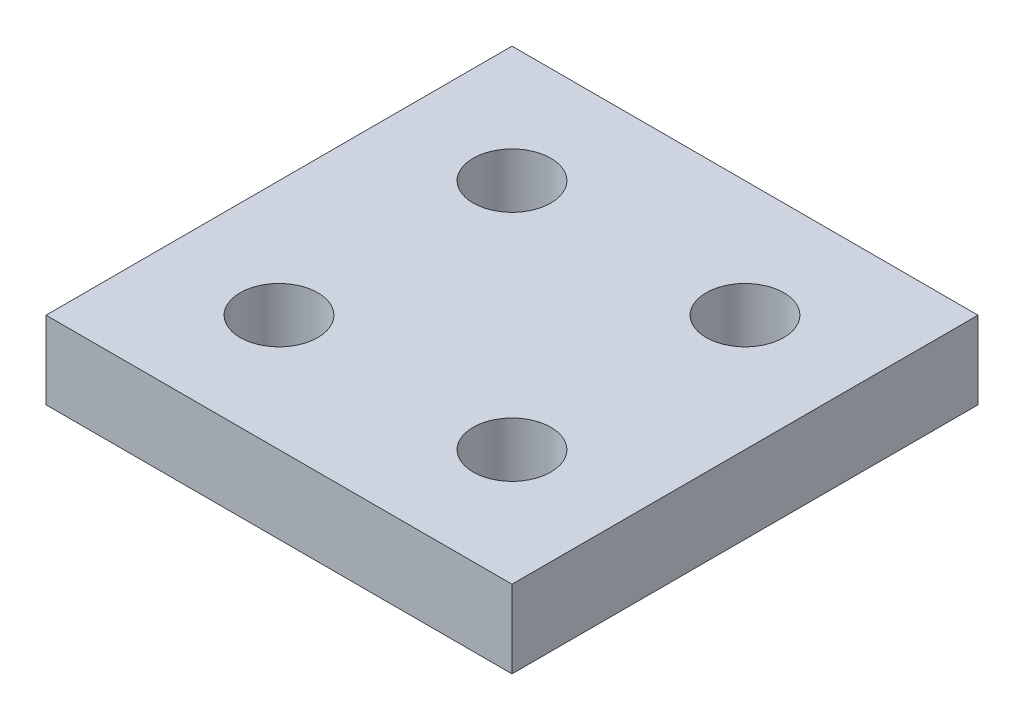
SolidWorks part; units mm, degrees
ref_plane "Front Plane" through (0, 0, 0) normal (0, 0, 1) x (1, 0, 0)
ref_plane "Top Plane" through (0, 0, 0) normal (0, 1, 0) x (1, 0, 0)
ref_plane "Right Plane" through (0, 0, 0) normal (1, 0, 0) x (0, 0, -1)
sketch "Sketch1" plane through (0, 0, 0) normal (0, 1, 0) x (1, 0, 0)
  line L0 (0, 0) -> (60, 0)
  line L1 (60, 0) -> (60, 60)
  line L2 (60, 60) -> (0, 60)
  line L3 (0, 60) -> (0, 0)
  circle A0 centre (15, 45) radius 5
  circle A1 centre (45, 45) radius 5
  circle A2 centre (45, 15) radius 5
  circle A3 centre (15, 15) radius 5
  dimension "D3" = 10
  dimension "D5" = 15
  dimension "D1" = 60
  dimension "D2" = 60
  dimension "D4" = 15
  dimension "D6" = 2
  dimension "D7" = 2
extrude "Boss-Extrude1" add sketch "Sketch1" along normal blind 10
